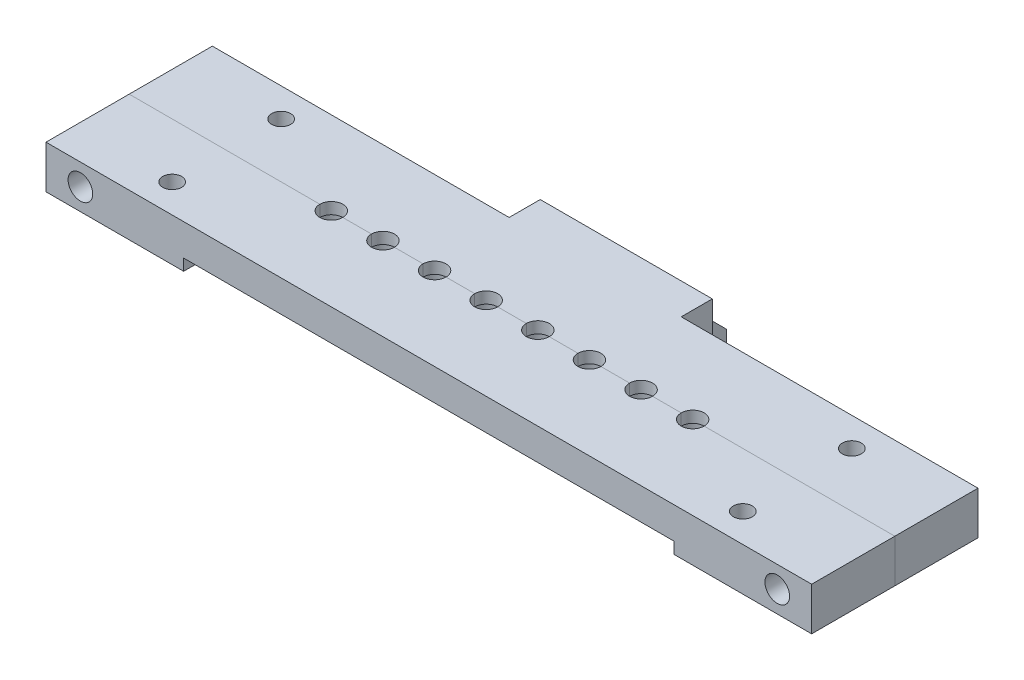
SolidWorks part; units mm, degrees
ref_plane "Front Plane" through (0, 0, 0) normal (0, 0, 1) x (1, 0, 0)
ref_plane "Top Plane" through (0, 0, 0) normal (0, 1, 0) x (1, 0, 0)
ref_plane "Right Plane" through (0, 0, 0) normal (1, 0, 0) x (0, 0, -1)
sketch "Sketch1" plane through (0, 0, 0) normal (0, 0, 1) x (1, 0, 0)
  line L0 (-31.5, 3.75) -> (-31.5, -3.75) construction
  line L1 (54.74, -3.75) -> (-54.74, -3.75)
  line L2 (54.74, -3.75) -> (54.74, 3.75)
  line L3 (54.74, 3.75) -> (-54.74, 3.75)
  line L4 (-54.74, -3.75) -> (-54.74, 3.75)
  line L5 (54.74, -3.75) -> (-54.74, 3.75) construction
  line L6 (54.74, 3.75) -> (-54.74, -3.75) construction
  line L7 (-33.5, 3.75) -> (-33.5, 1.75)
  line L8 (-33.5, -1.25) -> (-34.25, -1.25)
  line L9 (-34.25, -1.25) -> (-34.25, 1.75)
  line L10 (-34.25, 1.75) -> (-33.5, 1.75)
  line L11 (-33.5, -1.25) -> (-33.5, -2.25)
  line L12 (-33.5, -2.25) -> (-35.4, -2.25)
  line L13 (-35.4, -2.25) -> (-35.4, -3.75)
  point P0 (0, 0)
  point P17 (-34.25, 0.25)
  dimension "D1" = 109.48
  dimension "D2" = 23.24
  dimension "D3" = 5.5
  dimension "D4" = 4
  dimension "D5" = 7.8
  dimension "D6" = 4
  dimension "D7" = 3
  dimension "D8" = 2
  dimension "D9" = 1
extrude "Boss-Extrude1" add sketch "Sketch1" along normal mid plane 29 contours L13 L12 L11 L8 L9 L10 L7 L3 L4 L1 | L12 L13 L1 L2 L3 L7 L10 L9 L8 L11
sketch "Sketch2" plane through (0, 0, 0) normal (0, 0, 1) x (1, 0, 0)
  line L0 (-31.5, 3.75) -> (-31.5, -3.75) construction
  line L1 (-35.4, -2.25) -> (-35.4, -3.75) construction
  line L2 (-33.5, -2.25) -> (-35.4, -2.25) construction
  line L3 (-33.5, -1.25) -> (-33.5, -2.25) construction
  line L4 (-33.5, -1.25) -> (-34.25, -1.25) construction
  line L5 (-34.25, -1.25) -> (-34.25, 1.75) construction
  line L6 (-34.25, 1.75) -> (-33.5, 1.75) construction
  line L7 (-33.5, 3.75) -> (-33.5, 1.75) construction
  line L8 (-31.5, 3.75) -> (-31.5, -3.75)
  line L9 (-35.4, -2.25) -> (-35.4, -3.75)
  line L10 (-33.5, -2.25) -> (-35.4, -2.25)
  line L11 (-33.5, -1.25) -> (-33.5, -2.25)
  line L12 (-33.5, -1.25) -> (-34.25, -1.25)
  line L13 (-34.25, -1.25) -> (-34.25, 1.75)
  line L14 (-34.25, 1.75) -> (-33.5, 1.75)
  line L15 (-33.5, 3.75) -> (-33.5, 1.75)
  line L16 (-33.5, 3.75) -> (-31.5, 3.75)
  line L17 (-31.5, -3.75) -> (-35.4, -3.75)
revolve "Cut-Revolve2" cut sketch "Sketch2" angle 360 about L8
pattern_linear "LPattern1" count 8 spacing 9 along (1, 0, 0) of "Cut-Revolve2"
sketch "Sketch4" plane through (0, 3.75, 0) normal (0, 1, 0) x (1, 0, 0)
  line L0 (54.74, 14.5) -> (-54.74, 14.5) construction
  line L1 (-54.74, -14.5) -> (-54.74, 14.5) construction
  line L2 (54.74, -14.5) -> (-54.74, -14.5) construction
  line L3 (54.74, -14.5) -> (54.74, 14.5) construction
  circle A0 centre (-49.74, 9.5) radius 1.65
  circle A1 centre (49.74, 9.5) radius 1.65
  circle A2 centre (49.74, -9.5) radius 1.65
  circle A3 centre (-49.74, -9.5) radius 1.65
  dimension "D4" = 3.3
  dimension "D1" = 5
  dimension "D2" = 5
  dimension "D3" = 5
  dimension "D5" = 5
  dimension "D6" = 5
extrude "Cut-Extrude1" cut sketch "Sketch4" against normal up to surface (7.5 mm away) up to face at (31.5, -3.75, 3.9)
sketch "Sketch5" plane through (0, -3.75, 0) normal (0, -1, 0) x (1, 0, 0)
  line L0 (54.74, 14.5) -> (-54.74, 14.5) construction
  line L1 (-42.74, 14.5) -> (42.74, 14.5)
  line L2 (-42.74, 14.5) -> (-42.74, 9.5)
  line L3 (-42.74, 9.5) -> (42.74, 9.5)
  line L4 (42.74, 14.5) -> (42.74, 9.5)
  line L5 (54.74, -14.5) -> (-54.74, -14.5) construction
  line L6 (-42.74, -14.5) -> (42.74, -14.5)
  line L7 (-42.74, -14.5) -> (-42.74, -9.5)
  line L8 (-42.74, -9.5) -> (42.74, -9.5)
  line L9 (42.74, -14.5) -> (42.74, -9.5)
  line L10 (-54.74, 14.5) -> (-54.74, -14.5) construction
  line L11 (54.74, 14.5) -> (54.74, -14.5) construction
  dimension "D1" = 5
  dimension "D2" = 12
  dimension "D3" = 12
extrude "Cut-Extrude2" cut sketch "Sketch5" against normal blind 2
sketch "Sketch7" plane through (0, 0, -14.5) normal (0, 0, -1) x (-1, 0, 0)
  line L0 (-54.74, 3.75) -> (54.74, 3.75) construction
  line L1 (-54.74, -3.75) -> (-66.74, -3.75)
  line L2 (-54.74, -3.75) -> (-54.74, 3.75)
  line L3 (-54.74, 3.75) -> (-66.74, 3.75)
  line L4 (-66.74, -3.75) -> (-66.74, 3.75)
  line L5 (54.74, -3.75) -> (66.74, -3.75)
  line L6 (54.74, -3.75) -> (54.74, 3.75)
  line L7 (54.74, 3.75) -> (66.74, 3.75)
  line L8 (66.74, -3.75) -> (66.74, 3.75)
  circle A0 centre (-60.74, 0) radius 2.15
  circle A1 centre (60.74, 0) radius 2.15
  point P15 (60.74, -3.75)
  point P17 (66.74, 0)
  point P24 (-60.74, 3.75)
  point P26 (-54.74, 0)
  dimension "D3" = 4.3
  dimension "D2" = 12
extrude "Boss-Extrude2" add sketch "Sketch7" against normal up to surface (29 mm away) up to face at (0, -1.375, 14.5)
sketch "Sketch8" plane through (0, 0, -14.5) normal (0, 0, -1) x (-1, 0, 0)
  line L0 (-66.74, 3.75) -> (66.74, 3.75) construction
  line L1 (-15, 3.75) -> (15, 3.75)
  line L2 (-15, 3.75) -> (-15, -1.75)
  line L3 (-15, -1.75) -> (15, -1.75)
  line L4 (15, 3.75) -> (15, -1.75)
  line L5 (42.74, -1.75) -> (-42.74, -1.75) construction
  point P8 (0, 3.75)
  point P9 (0, 3.75)
  dimension "D1" = 30
extrude "Boss-Extrude3" add sketch "Sketch8" along normal up to surface (5.42 mm away)
sketch "Sketch9" plane through (0, -1.75, 0) normal (0, -1, 0) x (1, 0, 0)
  line L0 (15, -19.92) -> (15, -14.5) construction
  line L1 (-15, -19.92) -> (15, -19.92) construction
  line L2 (-15, -19.92) -> (-15, -14.5) construction
  line L3 (15, -19.92) -> (15, -14.5)
  line L4 (-15, -19.92) -> (15, -19.92)
  line L5 (-15, -19.92) -> (-15, -14.5)
  line L6 (-15, -14.5) -> (15, -14.5)
extrude "Boss-Extrude4" add sketch "Sketch9" along normal up to surface (19.9135 mm away)
sketch "Sketch10" plane through (15, 0, 0) normal (1, 0, 0) x (0, 0, -1)
  line L0 (19.92, -21.6635) -> (19.92, 3.75) construction
  line L1 (14.5, -21.6635) -> (19.92, -21.6635)
  line L2 (14.5, -21.6635) -> (14.5, -16.6635)
  line L3 (14.5, -16.6635) -> (19.92, -16.6635)
  line L4 (19.92, -21.6635) -> (19.92, -16.6635)
  dimension "D1" = 5
extrude "Boss-Extrude5" add sketch "Sketch10" along normal blind 20 and the other way blind 50
sketch "Sketch11" plane through (0, -16.6635, 0) normal (0, 1, 0) x (1, 0, 0)
  line L1 (35, 19.92) -> (35, 14.5) construction
  line L2 (-35, 19.92) -> (-35, 14.5) construction
  circle A0 centre (-30, 17.21) radius 1.65
  circle A1 centre (30, 17.21) radius 1.65
  point P8 (35, 17.21)
  dimension "D1" = 3.3
  dimension "D2" = 5
  dimension "D3" = 5
extrude "Cut-Extrude3" cut sketch "Sketch11" against normal up to surface (5 mm away) up to face at (0, -21.6635, -17.21)
sketch "Sketch12" plane through (0, 0, -19.92) normal (0, 0, -1) x (-1, 0, 0)
  line L0 (35, -21.6635) -> (-35, -21.6635) construction
  line L1 (-35, -16.6635) -> (-25, -16.6635)
  line L2 (-35, -16.6635) -> (-35, -21.6635)
  line L3 (-35, -21.6635) -> (-25, -21.6635)
  line L4 (-25, -16.6635) -> (-25, -21.6635)
  line L5 (35, -16.6635) -> (15, -16.6635) construction
  line L6 (25, -16.6635) -> (35, -16.6635)
  line L7 (25, -16.6635) -> (25, -21.6635)
  line L8 (25, -21.6635) -> (35, -21.6635)
  line L9 (35, -16.6635) -> (35, -21.6635)
  dimension "D1" = 10
  dimension "D2" = 10
extrude "Boss-Extrude6" add sketch "Sketch12" along normal blind 5
sketch "Sketch13" plane through (0, 0, -14.5) normal (0, 0, 1) x (1, 0, 0)
  line L0 (35, -21.6635) -> (-35, -21.6635) construction
  line L1 (-35, -16.6635) -> (-25, -16.6635)
  line L2 (-35, -16.6635) -> (-35, -21.6635)
  line L3 (-35, -21.6635) -> (-25, -21.6635)
  line L4 (-25, -16.6635) -> (-25, -21.6635)
  line L5 (15, -16.6635) -> (35, -16.6635) construction
  line L6 (35, -21.6635) -> (25, -21.6635)
  line L7 (35, -21.6635) -> (35, -16.6635)
  line L8 (35, -16.6635) -> (25, -16.6635)
  line L9 (25, -21.6635) -> (25, -16.6635)
  line L10 (-25, -16.6635) -> (-25, -21.6635) construction
  line L11 (25, -21.6635) -> (25, -16.6635) construction
extrude "Boss-Extrude7" add sketch "Sketch13" along normal blind 5
chamfer "Chamfer1" distance 10 angle 45 2 edges at (-15, -16.6635, -17.21) (15, -16.6635, -17.21)
ref_plane "Plane1" through (0, 0, 0) normal (-1, 0, 0) x (0, 0, 1)
split "Split1" trim tools "Front Plane" bodies to split 114 resulting bodies 111 112
sketch "Sketch14" plane through (0, 0, 0) normal (-1, 0, 0) x (0, 0, 1)
  line L0 (-19.92, -6.6635) -> (-27.42, -14.1635)
  line L1 (-27.42, -14.1635) -> (-27.42, -39.6635)
  line L2 (-19.92, -6.6635) -> (-19.92, 3.75) construction
  line L4 (-27.42, -28.3761) -> (-27.42, -23.6635) construction
  line L6 (-19.92, -6.6635) -> (-19.92, 0.4075)
  line L7 (-19.92, 0.4075) -> (-32.42, -12.0925)
  line L8 (-32.42, -12.0925) -> (-32.42, -39.6635)
  line L9 (-32.42, -39.6635) -> (-27.42, -39.6635)
  point P9 (-27.42, -39.6635)
  dimension "D1" = 135
  dimension "D2" = 5
  dimension "D3" = 5
extrude "Boss-Extrude8" add sketch "Sketch14" along normal mid plane 10
sketch "Sketch15" plane through (0, 0, -32.42) normal (0, 0, -1) x (-1, 0, 0)
  line L0 (5, -39.6635) -> (-5, -39.6635) construction
  line L2 (-100, -32.7563) -> (170, -32.7563) construction
  line L3 (-100, -30.5708) -> (170, -30.5708) construction
  line L4 (-100, -32.7563) -> (170, -32.7563) construction
  line L5 (-100, -30.5708) -> (170, -30.5708) construction
  line L6 (0, -30.5708) -> (0, -32.7563) construction
  circle A0 centre (0, -31.6635) radius 1.65
  point P2 (0, -31.6635)
  point P6 (0, -39.6635)
  dimension "D1" = 3.3
extrude "Cut-Extrude4" cut sketch "Sketch15" against normal up to surface (5 mm away) contours A0 up to face at (0, -26.9135, -27.42)
ref_plane "Plane2" through (31.5, 0, 0) normal (1, 0, 0) x (0, 0, -1)
equation "\"Plate_height\"= 14.35mm'end to end plate height"
equation "\"Plate_width\"= 85.48mm'end to end plate width"
equation "\"Plate_length\"= 127.76mm'end to end plate length"
equation "\"hole_offset_length_side\"= 11.24mm'offset between well and length side "
equation "\"well2well_distance\"= 9mm'center to center/edge to edge separation between 2 wells"
equation "\"well_diameter\"= 7mm'well diameter"
equation "\"lensL_diameter\"= 3mm'lens diameter on LED side"
equation "\"lensL_height\"= 2mm'lens height on LED side"
equation "\"lensL_focal\"= 4mm'lens focal length on LED side"
equation "\"lensP_diameter\"= 5mm'lens diameter on photodiode side"
equation "\"lensP_height\"= 2mm'lens height on photodiode side"
equation "\"lensP_focal\"= 4mm'lens focal length on photodiode side"
equation "\"filter_length\"= 40mm'filter length"
equation "\"filter_width\"= 25mm'filter width"
equation "\"filter_thickness\"= 2mm'filter thickness"
equation "\"filter2filter_clearance\"= 1.5mm'wall thickness between both filters"
equation "\"LED_diameter\"= 3.45mm'bounding diameter of LED"
equation "\"photodiode_diameter\"= 2.9 * 2mm + 1'bounding diameter of photodiode with optical center aligned with diameter center. Dont forget to align the pcb photodiode with the optical center of your system"
equation "\"D1@Sketch1\"=\"Plate_width\"+2*2+10*2"
equation "\"D2@Sketch1\"=10+2+\"hole_offset_length_side\""
equation "\"D3@Sketch1\"=\"lensP_diameter\"+0.5"
equation "\"D5@Sketch1\"=\"photodiode_diameter\"+0.5*2"
equation "\"D6@Sketch1\"=\"lensL_focal\""
equation "\"D7@Sketch1\"=\"lensL_height\"+0.5*2"
equation "\"D1@Boss-Extrude1\"=\"well2well_distance\"+10*2"
equation "\"D3@LPattern1\"=\"well2well_distance\""
